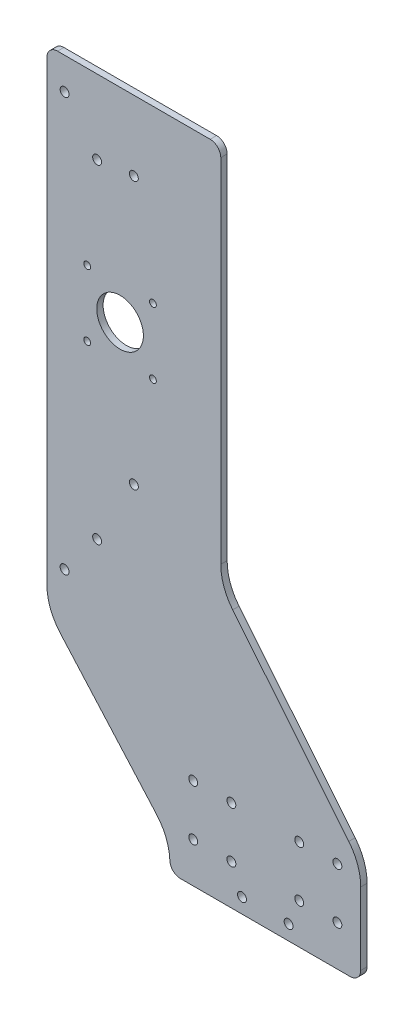
SolidWorks part; units mm, degrees
ref_plane "Front Plane" through (0, 0, 0) normal (0, 0, 1) x (1, 0, 0)
ref_plane "Top Plane" through (0, 0, 0) normal (0, 1, 0) x (1, 0, 0)
ref_plane "Right Plane" through (0, 0, 0) normal (1, 0, 0) x (0, 0, -1)
sketch "Sketch1" plane through (0, 0, 0) normal (0, 0, 1) x (1, 0, 0)
  line L0 (107, -145) -> (107, -110.8956)
  line L1 (102, -150) -> (21.9809, -150)
  line L2 (-41, 154) -> (-41, -61.5222)
  line L3 (41, 154) -> (41, -12.1044)
  line L4 (-36, 159) -> (36, 159)
  line L5 (101.3809, -95.1038) -> (46.6191, -27.8962)
  line L6 (-34.7167, -78.0958) -> (10.7167, -129.4042)
  arc A0 (102, -150) -> (107, -145) centre (102, -145) ccw
  arc A1 (107, -110.8956) -> (101.3809, -95.1038) centre (82, -110.8956) ccw
  circle A2 centre (96, -107) radius 2.1
  circle A3 centre (96, -131) radius 2.1
  circle A4 centre (78, -107) radius 2.1
  circle A5 centre (78, -131) radius 2.1
  circle A6 centre (46, -107) radius 2.1
  circle A7 centre (46, -131) radius 2.1
  circle A8 centre (28, -107) radius 2.1
  circle A9 centre (28, -131) radius 2.1
  arc A10 (-36, 159) -> (-41, 154) centre (-36, 154) ccw
  arc A11 (-41, -61.5222) -> (-34.7167, -78.0958) centre (-16, -61.5222) ccw
  arc A12 (41, 154) -> (36, 159) centre (36, 154) ccw
  arc A13 (41, -12.1044) -> (46.6191, -27.8962) centre (66, -12.1044) ccw
  arc A14 (16.9809, -145) -> (10.7167, -129.4042) centre (-8, -145.9778) ccw
  circle A15 centre (51, -143) radius 2.1
  circle A16 centre (73, -143) radius 2.1
  arc A17 (16.9809, -145) -> (21.9809, -150) centre (21.9809, -145) ccw
  circle A18 centre (0, 126) radius 2.1
  circle A19 centre (0, 0) radius 2.1
  circle A20 centre (-32.6667, 144) radius 2.1
  circle A21 centre (-17.3333, 124) radius 2.1
  circle A22 centre (-17.3333, -31) radius 2.1
  circle A23 centre (-32.6667, -51) radius 2.1
  circle A24 centre (-6.5, 63) radius 11
  circle A25 centre (-22, 78.5) radius 1.6
  circle A26 centre (9, 78.5) radius 1.6
  circle A27 centre (-22, 47.5) radius 1.6
  circle A28 centre (9, 47.5) radius 1.6
extrude "Boss-Extrude1" add sketch "Sketch1" along normal mid plane 3
